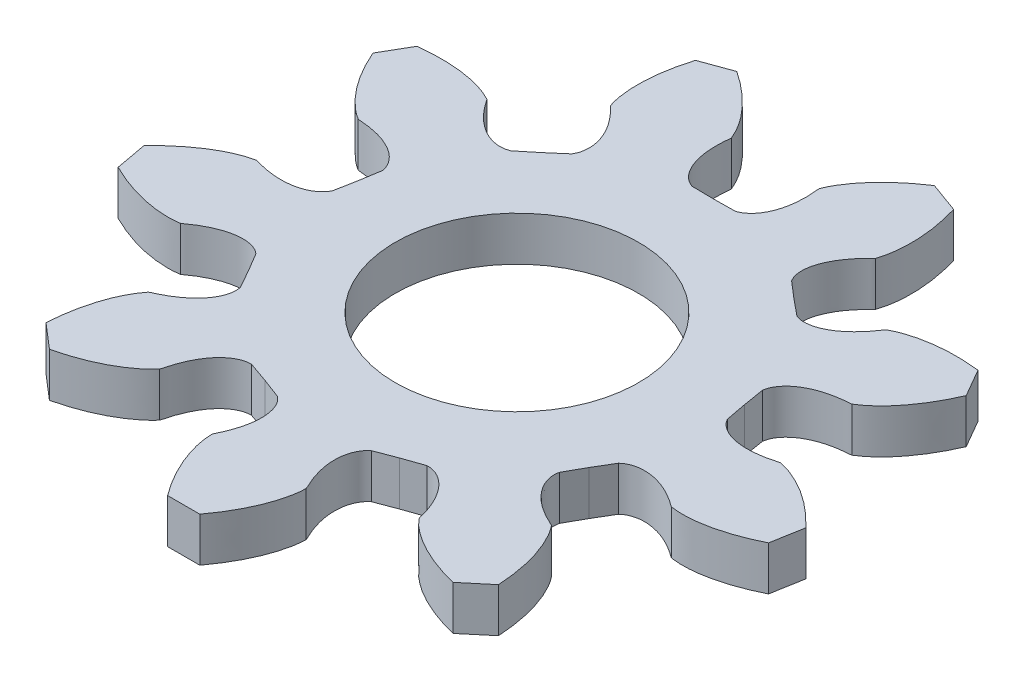
SolidWorks part; units mm, degrees
ref_plane "Plano frontal" through (0, 0, 0) normal (0, 0, 1) x (1, 0, 0)
ref_plane "Plano superior" through (0, 0, 0) normal (0, 1, 0) x (1, 0, 0)
ref_plane "Plano direito" through (0, 0, 0) normal (1, 0, 0) x (0, 0, -1)
sketch "Esboço1" plane through (0, 0, 0) normal (0, 1, 0) x (1, 0, 0)
  line L27 (-20.4895, -22.0869) -> (-18.2493, -24.0151)
  line L28 (-7.9319, -16.0554) -> (-6.0794, -16.703)
  line L29 (-6.0794, -16.703) -> (-4.244, -17.3977)
  line L30 (-1.4568, -30.1271) -> (1.4568, -30.1271)
  line L31 (4.244, -17.3977) -> (6.0794, -16.703)
  line L32 (6.0794, -16.703) -> (7.9319, -16.0554)
  line L33 (18.2493, -24.0151) -> (20.4813, -22.1423)
  line L34 (14.4341, -10.5994) -> (15.3936, -8.8875)
  line L35 (15.3936, -8.8875) -> (16.3964, -7.2006)
  line L36 (29.4164, -6.6662) -> (29.9224, -3.7968)
  line L37 (17.8703, 1.1584) -> (17.5049, 3.0866)
  line L38 (17.5049, 3.0866) -> (17.1888, 5.0235)
  line L39 (26.8192, 13.8019) -> (25.3624, 16.3252)
  line L40 (12.9449, 12.3742) -> (11.4255, 13.6164)
  line L41 (11.4255, 13.6164) -> (9.9384, 14.897)
  line L42 (11.673, 27.812) -> (8.9351, 28.8085)
  line L43 (1.9623, 17.8) -> (0, 17.775)
  line L44 (0, 17.775) -> (-1.9623, 17.8)
  line L45 (-8.9351, 28.8085) -> (-11.673, 27.812)
  line L46 (-9.9384, 14.897) -> (-11.4255, 13.6164)
  line L47 (-11.4255, 13.6164) -> (-12.9449, 12.3742)
  line L48 (-25.3624, 16.3252) -> (-26.8192, 13.8019)
  line L49 (-17.1888, 5.0235) -> (-17.5049, 3.0866)
  line L50 (-17.5049, 3.0866) -> (-17.8703, 1.1584)
  line L51 (-29.9224, -3.7968) -> (-29.3991, -6.6568)
  line L52 (-16.3964, -7.2006) -> (-15.3936, -8.8875)
  line L53 (-15.3936, -8.8875) -> (-14.4592, -10.5546)
  circle A1 centre (0, 0) radius 11
  spline S72 degree 3 poles (-18.2536, -15.0652) (-18.6426, -15.5464) (-19.2694, -16.6263) (-20.1291, -18.9736) (-20.4152, -20.8427) (-20.4895, -22.0869) knots 0.002191 0.002191 0.002191 0.002191 0.249989 0.497786 0.993382 0.993382 0.993382 0.993382
  spline S73 degree 3 poles (-18.2493, -24.0151) (-17.0371, -23.7259) (-15.246, -23.1195) (-13.0837, -21.8653) (-12.129, -21.0605) (-11.7227, -20.5939) knots 0.006618 0.006618 0.006618 0.006618 0.502214 0.750011 0.997809 0.997809 0.997809 0.997809
  spline S74 degree 3 poles (-11.7227, -20.5939) (-11.6757, -20.4784) (-11.6235, -20.2386) (-11.4814, -19.7268) (-11.1823, -18.8582) (-10.5851, -17.6802) (-9.6866, -16.6682) (-8.8679, -16.2171) (-8.3328, -16.0639) (-8.0659, -16.0593) (-7.9319, -16.0554) knots 0.002676 0.002676 0.002676 0.002676 0.065194 0.127712 0.252749 0.502822 0.752894 0.877931 0.940449 1.002967 1.002967 1.002967 1.002967
  spline S75 degree 3 poles (-4.244, -17.3977) (-4.1439, -17.4868) (-3.9424, -17.6619) (-3.631, -18.1231) (-3.2937, -18.995) (-3.256, -20.3478) (-3.5557, -21.634) (-3.8849, -22.4917) (-4.105, -22.9751) (-4.2191, -23.1924) (-4.2574, -23.311) knots -0.002967 -0.002967 -0.002967 -0.002967 0.059551 0.122069 0.247106 0.497178 0.747251 0.872288 0.934806 0.997324 0.997324 0.997324 0.997324
  spline S76 degree 3 poles (-4.2574, -23.311) (-4.2461, -23.9296) (-4.0321, -25.1598) (-3.1819, -27.5105) (-2.1995, -29.1263) (-1.4568, -30.1271) knots 0.002191 0.002191 0.002191 0.002191 0.249989 0.497786 0.993382 0.993382 0.993382 0.993382
  spline S77 degree 3 poles (1.4568, -30.1271) (2.1995, -29.1263) (3.1819, -27.5105) (4.0321, -25.1598) (4.2461, -23.9296) (4.2574, -23.311) knots 0.006618 0.006618 0.006618 0.006618 0.502214 0.750011 0.997809 0.997809 0.997809 0.997809
  spline S78 degree 3 poles (4.2574, -23.311) (4.2191, -23.1924) (4.105, -22.9751) (3.8849, -22.4917) (3.5557, -21.634) (3.256, -20.3478) (3.2937, -18.995) (3.631, -18.1231) (3.9424, -17.6619) (4.1439, -17.4868) (4.244, -17.3977) knots 0.002676 0.002676 0.002676 0.002676 0.065194 0.127712 0.252749 0.502822 0.752894 0.877931 0.940449 1.002967 1.002967 1.002967 1.002967
  spline S79 degree 3 poles (7.9319, -16.0554) (8.0658, -16.0593) (8.3328, -16.0639) (8.8679, -16.2171) (9.6866, -16.6682) (10.5851, -17.6802) (11.1823, -18.8582) (11.4814, -19.7268) (11.6235, -20.2386) (11.6757, -20.4784) (11.7227, -20.5939) knots -0.002967 -0.002967 -0.002967 -0.002967 0.059551 0.122069 0.247106 0.497178 0.747251 0.872288 0.934806 0.997324 0.997324 0.997324 0.997324
  spline S80 degree 3 poles (11.7227, -20.5939) (12.129, -21.0605) (13.0837, -21.8653) (15.246, -23.1195) (17.0371, -23.7259) (18.2493, -24.0151) knots 0.002191 0.002191 0.002191 0.002191 0.249989 0.497786 0.993382 0.993382 0.993382 0.993382
  spline S81 degree 3 poles (20.4813, -22.1423) (20.407, -20.8982) (20.1208, -19.029) (19.2611, -16.6818) (18.6343, -15.6018) (18.2454, -15.1207) knots 0.006618 0.006618 0.006618 0.006618 0.502214 0.750011 0.997809 0.997809 0.997809 0.997809
  spline S82 degree 3 poles (18.2454, -15.1207) (18.1398, -15.0544) (17.9127, -14.9613) (17.4334, -14.7325) (16.6299, -14.2871) (15.5736, -13.4944) (14.7329, -12.4339) (14.4308, -11.5492) (14.3729, -10.9957) (14.4147, -10.732) (14.4341, -10.5994) knots 0.002676 0.002676 0.002676 0.002676 0.065194 0.127712 0.252749 0.502822 0.752894 0.877931 0.940449 1.002967 1.002967 1.002967 1.002967
  spline S83 degree 3 poles (16.3964, -7.2006) (16.5015, -7.1175) (16.709, -6.9495) (17.2173, -6.7228) (18.1345, -6.5422) (19.4733, -6.7399) (20.6879, -7.2584) (21.4754, -7.7315) (21.9133, -8.0322) (22.1074, -8.1824) (22.2176, -8.2407) knots -0.002967 -0.002967 -0.002967 -0.002967 0.059551 0.122069 0.247106 0.497178 0.747251 0.872288 0.934806 0.997324 0.997324 0.997324 0.997324
  spline S84 degree 3 poles (22.2176, -8.2407) (22.8287, -8.3369) (24.0774, -8.3398) (26.54, -7.9107) (28.3018, -7.2239) (29.4164, -6.6662) knots 0.002191 0.002191 0.002191 0.002191 0.249989 0.497786 0.993382 0.993382 0.993382 0.993382
  spline S85 degree 3 poles (29.9224, -3.7968) (29.0657, -2.8916) (27.6451, -1.6436) (25.4777, -0.3981) (24.3034, 0.0263) (23.6962, 0.1448) knots 0.006618 0.006618 0.006618 0.006618 0.502214 0.750011 0.997809 0.997809 0.997809 0.997809
  spline S86 degree 3 poles (23.6962, 0.1448) (23.5727, 0.1277) (23.3389, 0.0531) (22.8246, -0.0798) (21.9228, -0.2551) (20.6041, -0.3268) (19.2784, -0.0548) (18.4783, 0.4287) (18.0782, 0.8155) (17.9407, 1.0444) (17.8703, 1.1584) knots 0.002676 0.002676 0.002676 0.002676 0.065194 0.127712 0.252749 0.502822 0.752894 0.877931 0.940449 1.002967 1.002967 1.002967 1.002967
  spline S87 degree 3 poles (17.1888, 5.0235) (17.2159, 5.1546) (17.2669, 5.4167) (17.5106, 5.9171) (18.097, 6.645) (19.2497, 7.3541) (20.5135, 7.7377) (21.4209, 7.8814) (21.9495, 7.9325) (22.1948, 7.9423) (22.3167, 7.9685) knots -0.002967 -0.002967 -0.002967 -0.002967 0.059551 0.122069 0.247106 0.497178 0.747251 0.872288 0.934806 0.997324 0.997324 0.997324 0.997324
  spline S88 degree 3 poles (22.3167, 7.9685) (22.8467, 8.2876) (23.8051, 9.088) (25.4157, 10.9997) (26.3239, 12.6583) (26.8192, 13.8019) knots 0.002191 0.002191 0.002191 0.002191 0.249989 0.497786 0.993382 0.993382 0.993382 0.993382
  spline S89 degree 3 poles (25.3624, 16.3252) (24.1243, 16.468) (22.2339, 16.5108) (19.773, 16.0718) (18.6006, 15.642) (18.0592, 15.3426) knots 0.006618 0.006618 0.006618 0.006618 0.502214 0.750011 0.997809 0.997809 0.997809 0.997809
  spline S90 degree 3 poles (18.0592, 15.3426) (17.9756, 15.2501) (17.8445, 15.0426) (17.536, 14.6103) (16.9578, 13.8963) (15.9937, 12.9937) (14.8033, 12.35) (13.8796, 12.2061) (13.3245, 12.2452) (13.072, 12.3321) (12.9449, 12.3742) knots 0.002676 0.002676 0.002676 0.002676 0.065194 0.127712 0.252749 0.502822 0.752894 0.877931 0.940449 1.002967 1.002967 1.002967 1.002967
  spline S91 degree 3 poles (9.9384, 14.897) (9.8748, 15.0149) (9.7454, 15.2484) (9.6105, 15.7883) (9.5918, 16.723) (10.019, 18.0071) (10.7405, 19.1132) (11.3433, 19.8066) (11.7154, 20.1856) (11.897, 20.3507) (11.9735, 20.4491) knots -0.002967 -0.002967 -0.002967 -0.002967 0.059551 0.122069 0.247106 0.497178 0.747251 0.872288 0.934806 0.997324 0.997324 0.997324 0.997324
  spline S92 degree 3 poles (11.9735, 20.4491) (12.1744, 21.0342) (12.3941, 22.2634) (12.3991, 24.7632) (12.0287, 26.6175) (11.673, 27.812) knots 0.002191 0.002191 0.002191 0.002191 0.249989 0.497786 0.993382 0.993382 0.993382 0.993382
  spline S93 degree 3 poles (8.9351, 28.8085) (7.8949, 28.122) (6.4192, 26.9397) (4.8163, 25.0215) (4.1944, 23.9387) (3.9722, 23.3613) knots 0.006618 0.006618 0.006618 0.006618 0.502214 0.750011 0.997809 0.997809 0.997809 0.997809
  spline S94 degree 3 poles (3.9722, 23.3613) (3.9676, 23.2367) (4.0005, 22.9935) (4.042, 22.464) (4.0581, 21.5455) (3.8997, 20.2343) (3.4016, 18.976) (2.7865, 18.272) (2.3361, 17.9451) (2.0868, 17.8495) (1.9623, 17.8) knots 0.002676 0.002676 0.002676 0.002676 0.065194 0.127712 0.252749 0.502822 0.752894 0.877931 0.940449 1.002967 1.002967 1.002967 1.002967
  spline S95 degree 3 poles (-1.9623, 17.8) (-2.0868, 17.8495) (-2.3361, 17.9451) (-2.7865, 18.272) (-3.4016, 18.976) (-3.8997, 20.2343) (-4.0581, 21.5455) (-4.042, 22.464) (-4.0005, 22.9935) (-3.9676, 23.2367) (-3.9722, 23.3613) knots -0.002967 -0.002967 -0.002967 -0.002967 0.059551 0.122069 0.247106 0.497178 0.747251 0.872288 0.934806 0.997324 0.997324 0.997324 0.997324
  spline S96 degree 3 poles (-3.9722, 23.3613) (-4.1944, 23.9387) (-4.8163, 25.0215) (-6.4192, 26.9397) (-7.8949, 28.122) (-8.9351, 28.8085) knots 0.002191 0.002191 0.002191 0.002191 0.249989 0.497786 0.993382 0.993382 0.993382 0.993382
  spline S97 degree 3 poles (-11.673, 27.812) (-12.0287, 26.6175) (-12.3991, 24.7632) (-12.3941, 22.2634) (-12.1744, 21.0342) (-11.9735, 20.4491) knots 0.006618 0.006618 0.006618 0.006618 0.502214 0.750011 0.997809 0.997809 0.997809 0.997809
  spline S98 degree 3 poles (-11.9735, 20.4491) (-11.897, 20.3507) (-11.7154, 20.1856) (-11.3432, 19.8066) (-10.7405, 19.1132) (-10.019, 18.0071) (-9.5918, 16.723) (-9.6105, 15.7883) (-9.7454, 15.2484) (-9.8748, 15.0149) (-9.9384, 14.897) knots 0.002676 0.002676 0.002676 0.002676 0.065194 0.127712 0.252749 0.502822 0.752894 0.877931 0.940449 1.002967 1.002967 1.002967 1.002967
  spline S99 degree 3 poles (-12.9449, 12.3742) (-13.072, 12.3321) (-13.3245, 12.2452) (-13.8796, 12.2061) (-14.8033, 12.35) (-15.9937, 12.9937) (-16.9578, 13.8963) (-17.536, 14.6103) (-17.8445, 15.0426) (-17.9756, 15.2501) (-18.0592, 15.3426) knots -0.002967 -0.002967 -0.002967 -0.002967 0.059551 0.122069 0.247106 0.497178 0.747251 0.872288 0.934806 0.997324 0.997324 0.997324 0.997324
  spline S100 degree 3 poles (-18.0592, 15.3426) (-18.6006, 15.642) (-19.773, 16.0718) (-22.2339, 16.5108) (-24.1243, 16.468) (-25.3624, 16.3252) knots 0.002191 0.002191 0.002191 0.002191 0.249989 0.497786 0.993382 0.993382 0.993382 0.993382
  spline S101 degree 3 poles (-26.8192, 13.8019) (-26.3239, 12.6583) (-25.4157, 10.9997) (-23.8051, 9.088) (-22.8467, 8.2876) (-22.3167, 7.9685) knots 0.006618 0.006618 0.006618 0.006618 0.502214 0.750011 0.997809 0.997809 0.997809 0.997809
  spline S102 degree 3 poles (-22.3167, 7.9685) (-22.1948, 7.9423) (-21.9495, 7.9325) (-21.4209, 7.8814) (-20.5135, 7.7377) (-19.2497, 7.3541) (-18.097, 6.645) (-17.5106, 5.9171) (-17.2669, 5.4167) (-17.2159, 5.1546) (-17.1888, 5.0235) knots 0.002676 0.002676 0.002676 0.002676 0.065194 0.127712 0.252749 0.502822 0.752894 0.877931 0.940449 1.002967 1.002967 1.002967 1.002967
  spline S103 degree 3 poles (-17.8703, 1.1584) (-17.9407, 1.0444) (-18.0782, 0.8155) (-18.4783, 0.4287) (-19.2784, -0.0548) (-20.6041, -0.3268) (-21.9228, -0.2551) (-22.8246, -0.0798) (-23.3389, 0.0531) (-23.5727, 0.1277) (-23.6962, 0.1448) knots -0.002967 -0.002967 -0.002967 -0.002967 0.059551 0.122069 0.247106 0.497178 0.747251 0.872288 0.934806 0.997324 0.997324 0.997324 0.997324
  spline S104 degree 3 poles (-23.6962, 0.1448) (-24.3034, 0.0263) (-25.4777, -0.3981) (-27.6451, -1.6436) (-29.0657, -2.8916) (-29.9224, -3.7968) knots 0.002191 0.002191 0.002191 0.002191 0.249989 0.497786 0.993382 0.993382 0.993382 0.993382
  spline S105 degree 3 poles (-29.3991, -6.6568) (-28.2845, -7.2145) (-26.5226, -7.9013) (-24.0599, -8.3304) (-22.8111, -8.3276) (-22.1999, -8.2313) knots 0.006571 0.006571 0.006571 0.006571 0.50219 0.75 0.997809 0.997809 0.997809 0.997809
  spline S106 degree 3 poles (-22.1999, -8.2313) (-22.0901, -8.1732) (-21.899, -8.02) (-21.4608, -7.7227) (-20.6754, -7.2519) (-19.463, -6.7374) (-18.1277, -6.5428) (-17.2146, -6.7237) (-16.708, -6.9502) (-16.5012, -7.1178) (-16.3964, -7.2006) knots 0.005881 0.005881 0.005881 0.005881 0.068199 0.130517 0.255153 0.504424 0.753696 0.878331 0.940649 1.002967 1.002967 1.002967 1.002967
  spline S107 degree 3 poles (-14.4592, -10.5546) (-14.4399, -10.6867) (-14.3982, -10.9496) (-14.4553, -11.5016) (-14.7552, -12.3828) (-15.5914, -13.4419) (-16.6432, -14.2347) (-17.4436, -14.6794) (-17.9201, -14.9103) (-18.1484, -14.9992) (-18.2536, -15.0652) knots -0.002967 -0.002967 -0.002967 -0.002967 0.059351 0.121669 0.246304 0.495576 0.744847 0.869483 0.931801 0.994119 0.994119 0.994119 0.994119
  point P77 (0, 0)
  dimension "D1" = 9
extrude "Ressalto-extrusão1" add sketch "Esboço1" along normal blind 4
